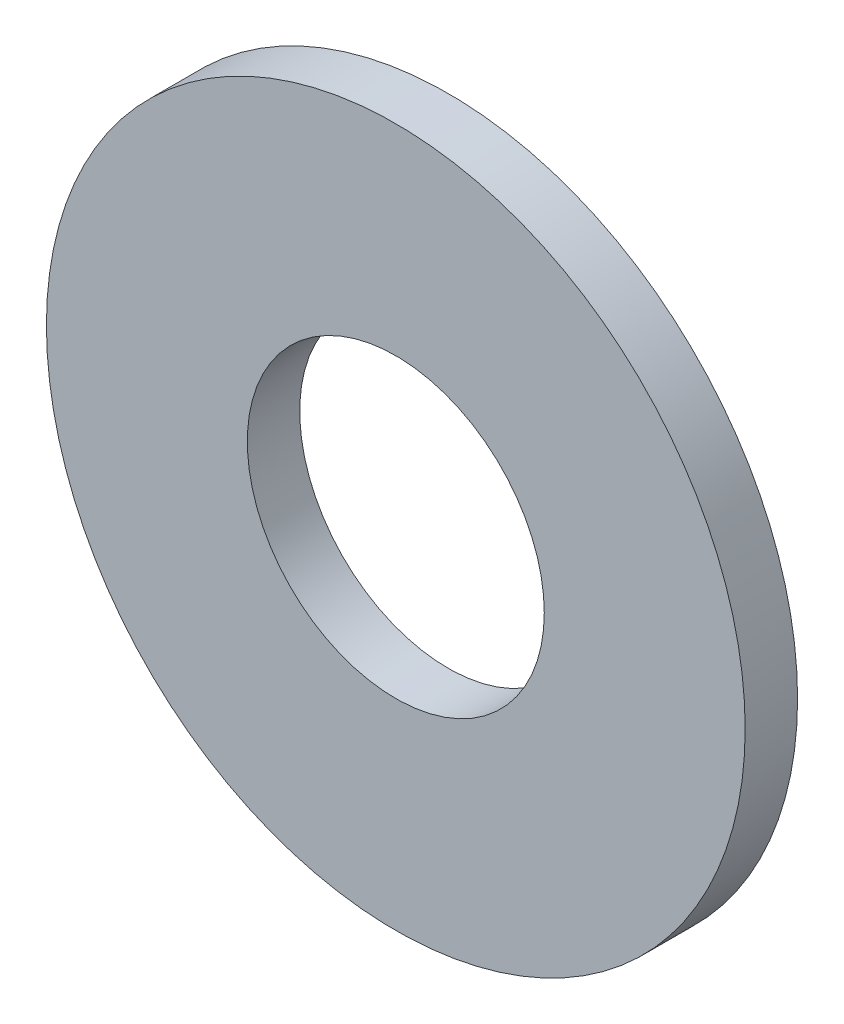
SolidWorks part; units mm, degrees
ref_plane "Front Plane" through (0, 0, 0) normal (0, 0, 1) x (1, 0, 0)
ref_plane "Top Plane" through (0, 0, 0) normal (0, 1, 0) x (1, 0, 0)
ref_plane "Right Plane" through (0, 0, 0) normal (1, 0, 0) x (0, 0, -1)
sketch "Sketch1" plane through (0, 0, 0) normal (0, 0, 1) x (1, 0, 0)
  circle A0 centre (0, 0) radius 4
  circle A1 centre (0, 0) radius 1.7
  dimension "D1" = 8
  dimension "D2" = 3.4
extrude "Boss-Extrude1" add sketch "Sketch1" along normal blind 0.6
